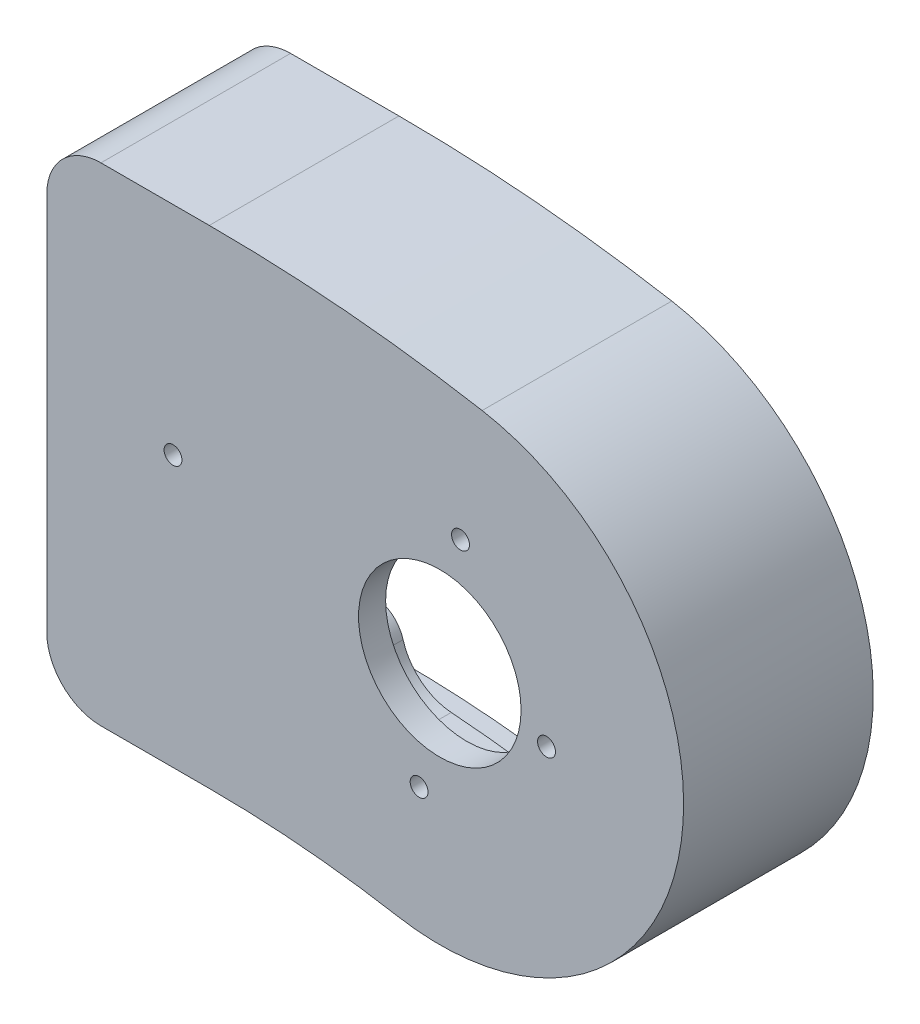
SolidWorks part; units mm, degrees
ref_plane "정면" through (0, 0, 0) normal (0, 0, 1) x (1, 0, 0)
ref_plane "윗면" through (0, 0, 0) normal (0, 1, 0) x (1, 0, 0)
ref_plane "우측면" through (0, 0, 0) normal (1, 0, 0) x (0, 0, -1)
sketch "스케치1" plane through (0, 0, 0) normal (0, 0, 1) x (1, 0, 0)
  line L0 (-1280.3224, 0) -> (-140.1612, 0) construction
  line L1 (-5, 45) -> (15, 45)
  line L2 (-15, 35) -> (-15, -35)
  line L3 (-5, -45) -> (15, -45)
  line L5 (-15, 45) -> (-13.4495, 40.3485) construction
  line L6 (-15, -45) -> (-13.4495, -40.3485) construction
  line L7 (15, -1502.5521) -> (15, -245) construction
  line L9 (0, 0) -> (58.2001, 0) construction
  line L10 (15, 45) -> (15, 50012.5521) construction
  line L11 (-1053.761, 0) -> (58.2001, 0) construction
  line L12 (102.3896, 0) -> (50000, 0) construction
  arc A0 (-15, -35) -> (-5, -45) centre (-5, -35) ccw
  arc A1 (-5, 45) -> (-15, 35) centre (-5, 35) ccw
  arc A2 (49.7296, -48.0384) -> (15, -45) centre (15, -245) ccw
  arc A4 (65.358, 40.5942) -> (15, 45) centre (15, -245) ccw
  arc A6 (49.7296, -48.0384) -> (65.358, 40.5942) centre (57.5438, -3.7221) ccw
  point P0 (0, 0)
  point P17 (15, -245)
  dimension "D3" = 10
  dimension "D5" = 400
  dimension "D1" = 90
  dimension "D2" = 30
  dimension "D4" = 200
extrude "보스-돌출1" add sketch "스케치1" along normal blind 35
sketch "스케치2" plane through (0, 0, 0) normal (0, 0, -1) x (-1, 0, 0)
  line L12 (-15, -40) -> (5, -40)
  line L13 (10, -35) -> (10, 35)
  line L14 (5, 40) -> (-15, 40)
  line L15 (-15, -40) -> (5, -40)
  line L16 (10, -35) -> (10, 35)
  line L17 (5, 40) -> (-15, 40)
  arc A20 (-15, -40) -> (-50.5979, -43.1144) centre (-15, -245) ccw
  arc A21 (5, -40) -> (10, -35) centre (5, -35) ccw
  arc A22 (10, 35) -> (5, 40) centre (5, 35) ccw
  arc A23 (-15, 40) -> (-64.4897, 35.6702) centre (-15, -245) ccw
  arc A24 (-64.4897, 35.6702) -> (-50.5979, -43.1144) centre (-57.5438, -3.7221) ccw
  arc A25 (-15, -40) -> (-50.5979, -43.1144) centre (-15, -245) ccw
  arc A26 (5, -40) -> (10, -35) centre (5, -35) ccw
  arc A27 (10, 35) -> (5, 40) centre (5, 35) ccw
  arc A28 (-15, 40) -> (-64.4897, 35.6702) centre (-15, -245) ccw
  arc A29 (-64.4897, 35.6702) -> (-50.5979, -43.1144) centre (-57.5438, -3.7221) ccw
  dimension "D1" = 5
extrude "컷-돌출1" cut sketch "스케치2" against normal blind 30
sketch "스케치3" plane through (-15, 0, 0) normal (-1, 0, 0) x (0, 0, 1)
  line L0 (0, 0) -> (50000, 0) construction
  line L1 (0, 0) -> (25000, 43301.2702) construction
  line L2 (0, 0) -> (25000, -43301.2702) construction
  line L3 (0, 35) -> (0, -35) construction
  circle A0 centre (0, 0) radius 20
  circle A1 centre (12.5, 21.6506) radius 2.25
  circle A2 centre (25, 0) radius 2.25
  circle A3 centre (12.5, -21.6506) radius 2.25
  dimension "D1" = 40
  dimension "D2" = 4.5
  dimension "D3" = 4.5
  dimension "D4" = 4.5
  dimension "D5" = 30
  dimension "D6" = 30
  dimension "D7" = 25
  dimension "D8" = 25
  dimension "D9" = 25
extrude "컷-돌출2" cut sketch "스케치3" against normal blind 5
sketch "스케치4" plane through (0, 0, 35) normal (0, 0, 1) x (1, 0, 0)
  line L0 (65.358, 40.5942) -> (-8617.0509, -49199.7934) construction
  line L1 (57.5438, -3.7221) -> (49297.9315, -8686.131) construction
  circle A0 centre (57.5438, -3.7221) radius 15
  circle A1 centre (61.3641, 17.9437) radius 2 construction
  circle A2 centre (53.7235, -25.3879) radius 2 construction
  circle A3 centre (77.24, -7.1951) radius 2 construction
  circle A4 centre (8.3034, 4.9603) radius 2 construction
  point P14 (0, 0)
  dimension "D1" = 30
  dimension "D3" = 4
  dimension "D4" = 4
  dimension "D5" = 4
  dimension "D9" = 4
  dimension "D2" = 45
  dimension "D6" = 22
  dimension "D7" = 20
  dimension "D8" = 22
  dimension "D10" = 50
extrude "컷-돌출3" cut sketch "스케치4" against normal up to next
sketch "스케치6" plane through (0, 0, 0) normal (0, 0, -1) x (-1, 0, 0)
  line L0 (10, 21.0271) -> (10, 19.0213)
  line L1 (10, 20) -> (10, -20) construction
  line L2 (10, 19.0213) -> (12, 19.0213)
  line L3 (12, 19.0213) -> (12, 21.0271)
  line L31 (12, -35) -> (12, -20)
  line L32 (-15, -42) -> (5, -42)
  line L33 (5, 42) -> (-15, 42)
  line L34 (12, 20) -> (12, 35)
  line L35 (12, -35) -> (12, -19.0815)
  line L36 (-15, -42) -> (5, -42)
  line L37 (5, 42) -> (-15, 42)
  line L38 (12, 21.0271) -> (12, 35)
  line L56 (10, -19.0815) -> (12, -19.0815)
  line L59 (10, -35) -> (10, -20)
  line L60 (-15, -40) -> (5, -40)
  line L61 (5, 40) -> (-15, 40)
  line L62 (10, 20) -> (10, 35)
  line L63 (10, -35) -> (10, -19.0815)
  line L64 (-15, -40) -> (5, -40)
  line L65 (5, 40) -> (-15, 40)
  line L66 (10, 21.0271) -> (10, 35)
  arc A34 (5, -42) -> (12, -35) centre (5, -35) ccw
  arc A35 (-15, -42) -> (-50.2506, -45.084) centre (-15, -245) ccw
  arc A36 (-64.837, 37.6398) -> (-50.2506, -45.084) centre (-57.5438, -3.7221) ccw
  arc A37 (-15, 42) -> (-64.837, 37.6398) centre (-15, -245) ccw
  arc A38 (12, 35) -> (5, 42) centre (5, 35) ccw
  arc A39 (5, -42) -> (12, -35) centre (5, -35) ccw
  arc A40 (-15, -42) -> (-50.2506, -45.084) centre (-15, -245) ccw
  arc A41 (-64.837, 37.6398) -> (-50.2506, -45.084) centre (-57.5438, -3.7221) ccw
  arc A42 (-15, 42) -> (-64.837, 37.6398) centre (-15, -245) ccw
  arc A43 (12, 35) -> (5, 42) centre (5, 35) ccw
  arc A69 (5, -40) -> (10, -35) centre (5, -35) ccw
  arc A70 (-15, -40) -> (-50.5979, -43.1144) centre (-15, -245) ccw
  arc A71 (-64.4897, 35.6702) -> (-50.5979, -43.1144) centre (-57.5438, -3.7221) ccw
  arc A72 (-15, 40) -> (-64.4897, 35.6702) centre (-15, -245) ccw
  arc A73 (10, 35) -> (5, 40) centre (5, 35) ccw
  arc A74 (5, -40) -> (10, -35) centre (5, -35) ccw
  arc A75 (-15, -40) -> (-50.5979, -43.1144) centre (-15, -245) ccw
  arc A76 (-64.4897, 35.6702) -> (-50.5979, -43.1144) centre (-57.5438, -3.7221) ccw
  arc A77 (-15, 40) -> (-64.4897, 35.6702) centre (-15, -245) ccw
  arc A78 (10, 35) -> (5, 40) centre (5, 35) ccw
  dimension "D1" = 2
  dimension "D2" = 0
extrude "컷-돌출5" cut sketch "스케치6" against normal blind 5
sketch "스케치8" plane through (0, 0, 30) normal (0, 0, -1) x (-1, 0, 0)
  line L0 (0.7139, 45) -> (50000.7139, 45) construction
  line L2 (15, -28.75) -> (15, 49971.25) construction
  line L3 (15, -20) -> (15, -35) construction
  line L5 (1.6218, -45) -> (50001.6218, -45) construction
  circle A0 centre (-15, 35) radius 6
  circle A1 centre (-15, -35) radius 6
  point P6 (15, -27.5)
  dimension "D1" = 12
  dimension "D2" = 12
  dimension "D3" = 10
  dimension "D4" = 30
  dimension "D5" = 10
  dimension "D6" = 30
extrude "보스-돌출2" add sketch "스케치8" along normal blind 25
sketch "스케치11" plane through (0, 0, 5) normal (0, 0, -1) x (-1, 0, 0)
  line L0 (-15, 35) -> (-15, -49965) construction
  line L1 (-56.0047, 35) -> (49943.9953, 35) construction
  line L2 (-60.2846, -35) -> (49939.7154, -35) construction
  circle A1 centre (-15, 35) radius 2
  circle A2 centre (-15, -35) radius 2
  dimension "D1" = 4
  dimension "D2" = 4
fillet "필렛1" radius 10 4 edges at (18.2768, -40.0262, 17.5) (11.6834, -40, 17.5) (11.6834, 40, 17.5) (18.346, 39.9804, 17.5)
hole_wizard "M4 나사 구멍2" positions "스케치16" profile "스케치15" tap size "M4" standard "ISO"
sketch "스케치16" plane through (0, 0, 30) normal (0, 0, -1) x (-1, 0, 0)
  point P0 (-61.3641, 17.9437)
  point P3 (-77.24, -7.1951)
  point P6 (-53.7235, -25.3879)
  point P11 (-8.3034, 4.9603)
sketch "스케치15" plane through (61.3641, 17.9437, 30) normal (1, 0, 0) x (0, 1, 0)
  line L0 (0, 0) -> (0, 12.4914)
  line L1 (0, 12.4914) -> (1.65, 11.5)
  line L2 (1.65, 11.5) -> (1.65, 0)
  line L5 (1.65, 0) -> (0, 0)
  line L10 (0, 12.4914) -> (-1.65, 11.5) construction
  line L11 (0, -6.35) -> (0, 107.95) construction
  dimension "탭 드릴 지름" = 3.3
  dimension "탭 드릴 깊이" = 11.5
  dimension "드릴 각도" = 118
cosmetic thread "구멍 나사산1" parameters "D1"=5, "D2"=4
cosmetic thread "구멍 나사산2" parameters "D1"=5, "D2"=4
cosmetic thread "구멍 나사산3" parameters "D1"=5, "D2"=4
cosmetic thread "구멍 나사산6" parameters "D1"=5, "D2"=4
hole_wizard "M4 나사 구멍3" positions "스케치17" profile "스케치18" tap size "M4" standard "ISO"
sketch "스케치17" plane through (0, 0, 5) normal (0, 0, -1) x (-1, 0, 0)
  point P0 (-15, 35)
  point P3 (-15, -35)
sketch "스케치18" plane through (15, 35, 5) normal (1, 0, 0) x (0, 1, 0)
  line L0 (0, 0) -> (0, 12.4914)
  line L1 (0, 12.4914) -> (1.65, 11.5)
  line L2 (1.65, 11.5) -> (1.65, 0)
  line L5 (1.65, 0) -> (0, 0)
  line L10 (0, 12.4914) -> (-1.65, 11.5) construction
  line L11 (0, -6.35) -> (0, 107.95) construction
  dimension "탭 드릴 지름" = 3.3
  dimension "탭 드릴 깊이" = 11.5
  dimension "드릴 각도" = 118
cosmetic thread "구멍 나사산4" parameters "D1"=8, "D2"=4
cosmetic thread "구멍 나사산5" parameters "D1"=8, "D2"=4
